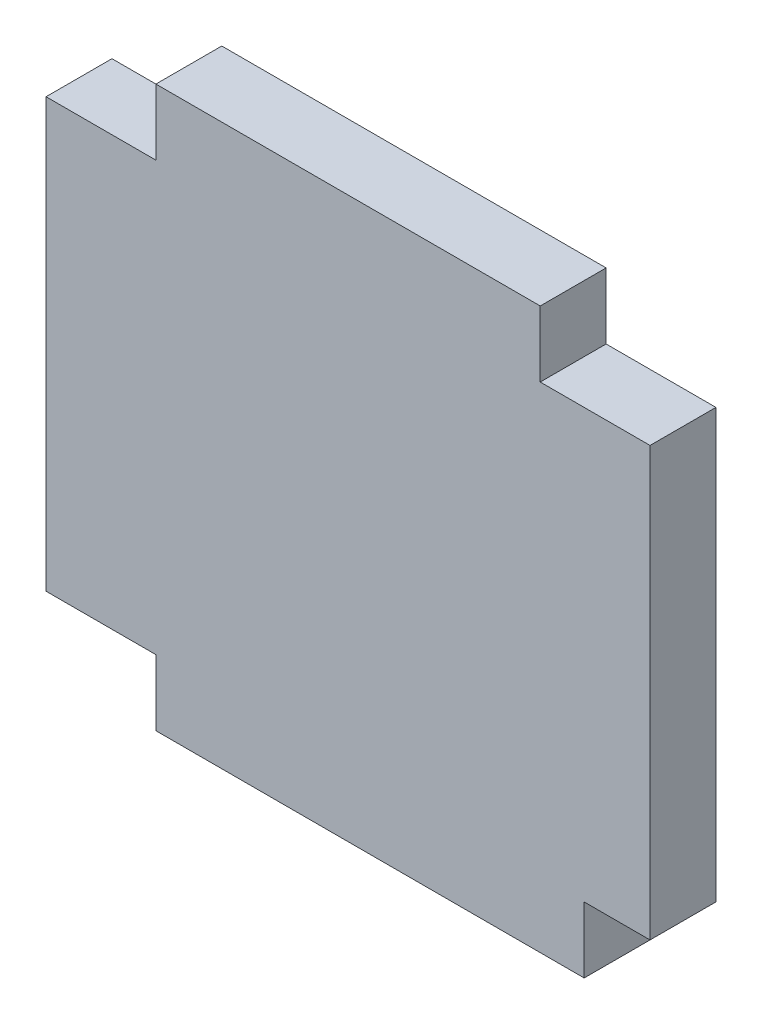
SolidWorks part; units mm, degrees
ref_plane "Front Plane" through (0, 0, 0) normal (0, 0, 1) x (1, 0, 0)
ref_plane "Top Plane" through (0, 0, 0) normal (0, 1, 0) x (1, 0, 0)
ref_plane "Right Plane" through (0, 0, 0) normal (1, 0, 0) x (0, 0, -1)
sketch "Sketch1" plane through (0, 0, 0) normal (0, 0, 1) x (1, 0, 0)
  line L1 (0, 45) -> (55, 45)
  line L2 (0, 45) -> (0, 0)
  line L3 (10, -6) -> (49, -6)
  line L4 (55, 45) -> (55, 0)
  line L7 (55, 0) -> (49, 0)
  line L8 (49, -6) -> (49, 0)
  line L11 (0, 0) -> (10, 0)
  line L12 (10, -6) -> (10, 0)
  point P1 (0, 0)
  dimension "D1" = 51
  dimension "D2" = 6
  dimension "D3" = 10
  dimension "D4" = 6
  dimension "D5" = 39
extrude "Boss-Extrude1" add sketch "Sketch1" along normal blind 6
sketch "Sketch2" plane through (0, 0, 6) normal (0, 0, 1) x (1, 0, 0)
  line L1 (0, 45) -> (10, 45)
  line L2 (0, 45) -> (0, 39)
  line L3 (0, 39) -> (10, 39)
  line L4 (10, 45) -> (10, 39)
  line L5 (55, 45) -> (45, 45)
  line L6 (55, 45) -> (55, 39)
  line L7 (55, 39) -> (45, 39)
  line L8 (45, 45) -> (45, 39)
  dimension "D1" = 6
  dimension "D2" = 10
  dimension "D3" = 10
  dimension "D4" = 6
extrude "Cut-Extrude1" cut sketch "Sketch2" against normal blind 6
